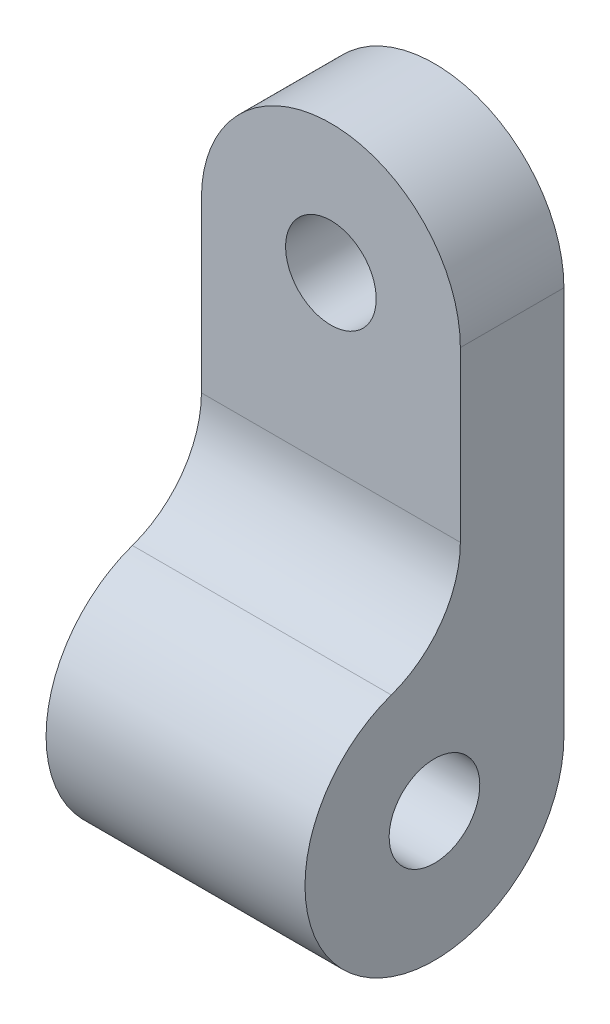
SolidWorks part; units mm, degrees
material "ABS"
ref_plane "Plano frontal" through (0, 0, 0) normal (0, 0, 1) x (1, 0, 0)
ref_plane "Plano superior" through (0, 0, 0) normal (0, 1, 0) x (1, 0, 0)
ref_plane "Plano direito" through (0, 0, 0) normal (1, 0, 0) x (0, 0, -1)
sketch "Esboço1" plane through (0, 0, 0) normal (0, 0, 1) x (1, 0, 0)
  line L0 (-5, 0) -> (-5, -20)
  line L3 (-5, -20) -> (5, -20)
  line L6 (5, -20) -> (5, 0)
  arc A0 (5, 0) -> (-5, 0) centre (0, 0) ccw
  circle A1 centre (0, 0) radius 1.75
  dimension "D1" = 3.5
  dimension "D2" = 10
  dimension "D3" = 20
extrude "Ressalto-extrusão1" add sketch "Esboço1" along normal blind 10
sketch "Esboço2" plane through (-5, 0, 0) normal (-1, 0, 0) x (0, 0, 1)
  line L0 (10, 0) -> (10, -20) construction
  line L1 (0, 0) -> (0, -20) construction
  line L2 (10, -20) -> (0, -20) construction
  line L3 (4, 5) -> (4, -6.5147)
  line L4 (10, 5) -> (0, 5) construction
  line L5 (4, 5) -> (10, 5)
  line L6 (10, 0) -> (10, 5) construction
  line L7 (10, 5) -> (10, -15)
  line L8 (10, -15) -> (10, -20)
  line L9 (10, -20) -> (0, -20)
  line L10 (0, -20) -> (0, -15)
  arc A0 (0, -15) -> (6.6667, -10.286) centre (5, -15) ccw
  circle A1 centre (5, -15) radius 1.75
  arc A2 (4, -6.5147) -> (6.6667, -10.286) centre (8, -6.5147) ccw
  line M2 (0, 0) -> (0, -20)
  line M3 (0, -20) -> (10, -20)
  line M4 (10, -20) -> (10, 0)
  line M5 (10, 0) -> (0, 0)
  dimension "D1" = 3.5
  dimension "D3" = 4
  dimension "D2" = 4
extrude "Corte-extrusão1" cut sketch "Esboço2" against normal blind 10 contours L3 A2 A0 M4 M5 | L7 L5 L3 M5 | A0 L9 M4 | A0 M2 M3 | A1
